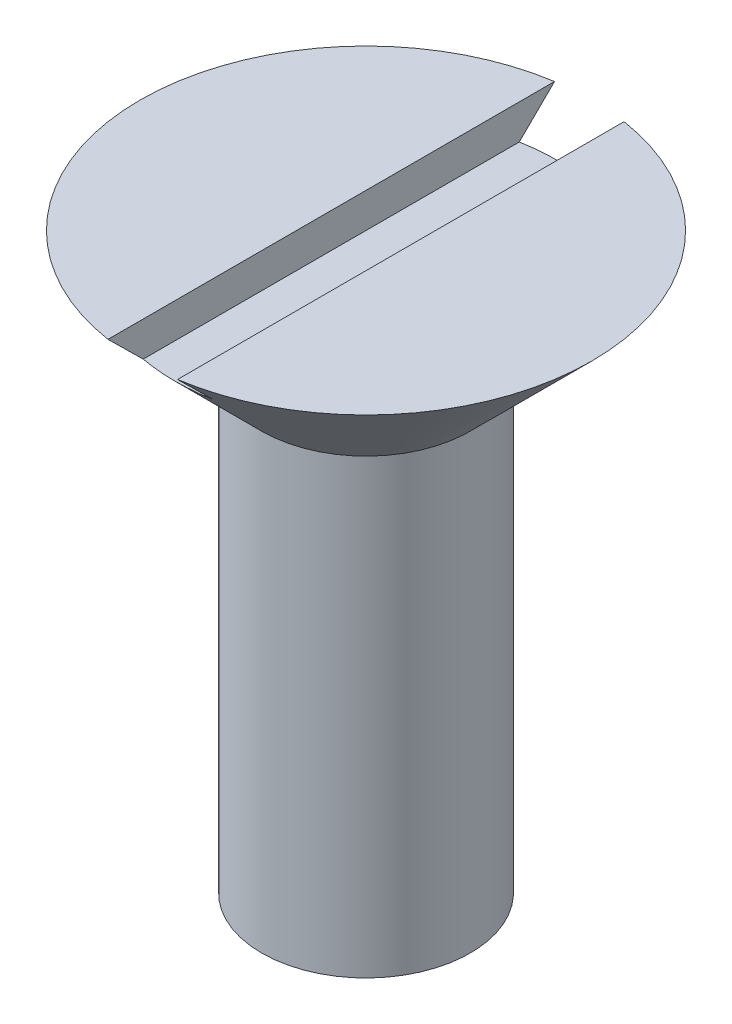
SolidWorks part; units mm, degrees
ref_plane "Front Plane" through (0, 0, 0) normal (0, 0, 1) x (1, 0, 0)
ref_plane "Top Plane" through (0, 0, 0) normal (0, 1, 0) x (1, 0, 0)
ref_plane "Right Plane" through (0, 0, 0) normal (1, 0, 0) x (0, 0, -1)
sketch "Sketch1" plane through (0, 0, 0) normal (0, 0, 1) x (1, 0, 0)
  line L0 (0, 0) -> (0, 157.9825) construction
  line L5 (3, 1.7321) -> (0, 0)
  line L7 (3, 1.7321) -> (3, 14.7321)
  line L8 (3, 14.7321) -> (6.5, 18.2321)
  line L9 (6.5, 18.2321) -> (0, 18.2321)
  line L10 (1.7008, 14.7321) -> (25.8781, 14.7321) construction
  line L11 (0, 18.2321) -> (0, 0)
  dimension "D1" = 3
  dimension "D2" = 13
  dimension "D3" = 120
  dimension "D4" = 45
  dimension "D5" = 6.5
revolve "Revolve1" add sketch "Sketch1" angle 360 about L11
sketch "Sketch2" plane through (0, 0, 0) normal (0, 0, 1) x (1, 0, 0)
  line L0 (6.5, 18.2321) -> (-6.5, 18.2321) construction
  line L1 (-1, 19.2321) -> (1, 19.2321)
  line L2 (-1, 19.2321) -> (-1, 17.2321)
  line L3 (-1, 17.2321) -> (1, 17.2321)
  line L4 (1, 19.2321) -> (1, 17.2321)
  point P4 (0, 17.2321)
  dimension "D1" = 1
  dimension "D2" = 2
  dimension "D3" = 2
extrude "Cut-Extrude1" cut sketch "Sketch2" against normal through all both and the other way through all
